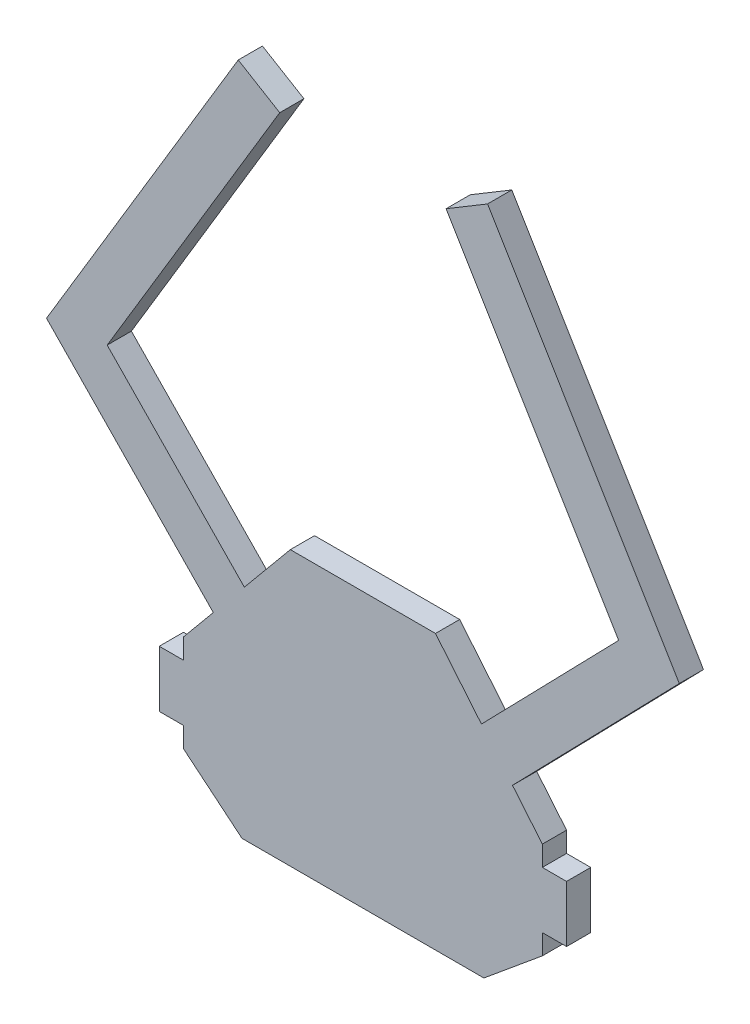
SolidWorks part; units mm, degrees
ref_plane "Alzado" through (0, 0, 0) normal (0, 0, 1) x (1, 0, 0)
ref_plane "Planta" through (0, 0, 0) normal (0, 1, 0) x (1, 0, 0)
ref_plane "Vista lateral" through (0, 0, 0) normal (1, 0, 0) x (0, 0, -1)
sketch "Croquis1" plane through (0, 0, 0) normal (0, 0, 1) x (1, 0, 0)
  line L0 (-25.25, 0) -> (0, 0) construction
  line L1 (22.25, 6) -> (-22.25, 6)
  line L2 (22.25, 6) -> (22.25, -6)
  line L3 (22.25, -6) -> (-22.25, -6)
  line L4 (-22.25, 6) -> (-22.25, -6)
  line L5 (22.25, 6) -> (-22.25, -6) construction
  line L6 (22.25, -6) -> (-22.25, 6) construction
  line L7 (22.25, 3.5) -> (25.25, 3.5)
  line L8 (22.25, 3.5) -> (22.25, -3.5)
  line L9 (22.25, -3.5) -> (25.25, -3.5)
  line L10 (25.25, 3.5) -> (25.25, -3.5)
  line L11 (-22.25, 3.5) -> (-25.25, 3.5)
  line L12 (-22.25, 3.5) -> (-22.25, -3.5)
  line L13 (-22.25, -3.5) -> (-25.25, -3.5)
  line L14 (-25.25, 3.5) -> (-25.25, -3.5)
  line L15 (-22.25, 6) -> (-9, 22)
  line L16 (-9, 22) -> (9, 22)
  line L17 (9, 22) -> (22.25, 6)
  line L18 (-22.25, -6) -> (-15, -12)
  line L19 (-15, -12) -> (15, -12)
  line L20 (15, -12) -> (22.25, -6)
  line L21 (0, 0) -> (0, -12) construction
  line L22 (0, 0) -> (0, 22) construction
  point P0 (0, 0)
  point P14 (25.25, 0)
  dimension "D1" = 7
  dimension "D2" = 7
  dimension "D3" = 3
  dimension "D4" = 3
  dimension "D5" = 44.5
  dimension "D6" = 34
  dimension "D7" = 30
  dimension "D8" = 12
  dimension "D9" = 6
  dimension "D10" = 18
extrude "Saliente-Extruir1" add sketch "Croquis1" along normal blind 3 contours L19 L20 L3 L18 | L1 L4 L3 L2 | L17 L16 L15 L1 | L10 L7 L2 L9 | L11 L14 L13 L4
sketch "Croquis2" plane through (0, 0, 3) normal (0, 0, 1) x (1, 0, 0)
  line L0 (0, 22) -> (0, 39.2551) construction
  line L1 (-9, 22) -> (9, 22) construction
  line L2 (0, 0) -> (-31.7086, 32.6072)
  line L3 (-31.7086, 32.6072) -> (-10.3134, 68.2644)
  line L4 (31.7086, 32.6072) -> (10.3134, 68.2644)
  line L5 (0, 0) -> (31.7086, 32.6072)
extrude "Extruir-Lámina1" add sketch "Croquis2" against normal through all thin thin type one direction wall 6
